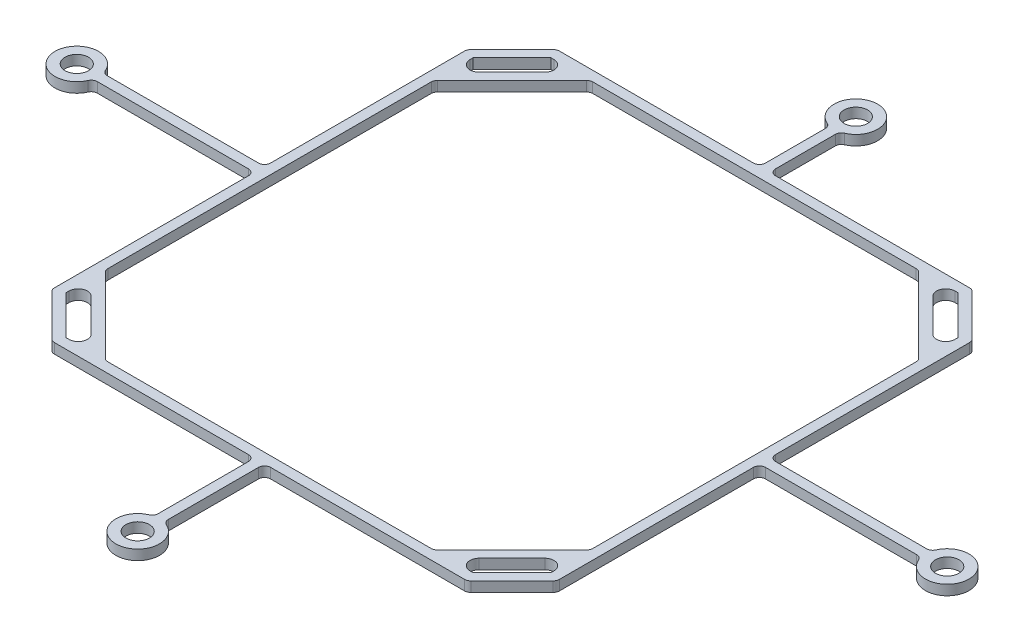
SolidWorks part; units mm, degrees
ref_plane "Front Plane" through (0, 0, 0) normal (0, 0, 1) x (1, 0, 0)
ref_plane "Top Plane" through (0, 0, 0) normal (0, 1, 0) x (1, 0, 0)
ref_plane "Right Plane" through (0, 0, 0) normal (1, 0, 0) x (0, 0, -1)
sketch "Sketch1" plane through (0, 0, 0) normal (0, 1, 0) x (1, 0, 0)
  line L0 (0, 0) -> (0, 56.4488) construction
  line L1 (0, 0) -> (-71.4488, 0) construction
  line L2 (-39.7988, 33.4083) -> (-33.4083, 39.7988)
  line L3 (-33.4083, -39.7988) -> (-29.2929, -39.7988)
  line L4 (-39.7988, -33.4083) -> (-39.7988, -29.2929)
  line L5 (-33.4083, 39.7988) -> (-29.2929, 39.7988)
  line L6 (39.7988, -33.4083) -> (39.7988, -29.2929)
  line L7 (-39.7988, -39.7988) -> (36.6035, 36.6035) construction
  line L8 (-36.6035, 36.6035) -> (39.7988, -39.7988) construction
  line L9 (33.4083, 39.7988) -> (39.7988, 33.4083)
  line L10 (39.7988, -33.4083) -> (33.4083, -39.7988)
  line L11 (-33.4083, -39.7988) -> (-39.7988, -33.4083)
  line L12 (-41.4488, 34.0917) -> (-34.0917, 41.4488)
  line L13 (34.0917, 41.4488) -> (0.825, 41.4488)
  line L14 (34.0917, 41.4488) -> (41.4488, 34.0917)
  line L15 (41.4488, -34.0917) -> (41.4488, -0.825)
  line L16 (41.4488, -34.0917) -> (34.0917, -41.4488)
  line L17 (-34.0917, -41.4488) -> (-0.825, -41.4488)
  line L18 (-34.0917, -41.4488) -> (-41.4488, -34.0917)
  line L19 (-41.4488, 34.0917) -> (-41.4488, 0.825)
  line L20 (-39.7988, 29.2929) -> (-29.2929, 39.7988)
  line L21 (-39.7988, 26.9594) -> (-26.9594, 39.7988)
  line L22 (29.2929, 39.7988) -> (39.7988, 29.2929)
  line L23 (26.9594, 39.7988) -> (39.7988, 26.9594)
  line L24 (39.7988, -29.2929) -> (29.2929, -39.7988)
  line L25 (39.7988, -26.9594) -> (26.9594, -39.7988)
  line L26 (-29.2929, -39.7988) -> (-39.7988, -29.2929)
  line L27 (-26.9594, -39.7988) -> (-39.7988, -26.9594)
  line L28 (-39.7988, 29.2929) -> (-39.7988, 33.4083)
  line L29 (-26.9594, 39.7988) -> (26.9594, 39.7988)
  line L30 (29.2929, 39.7988) -> (33.4083, 39.7988)
  line L31 (39.7988, 29.2929) -> (39.7988, 33.4083)
  line L32 (39.7988, -26.9594) -> (39.7988, 26.9594)
  line L33 (-39.7988, -26.9594) -> (-39.7988, 26.9594)
  line L34 (-26.9594, -39.7988) -> (26.9594, -39.7988)
  line L35 (29.2929, -39.7988) -> (33.4083, -39.7988)
  line L36 (67.9703, -0.825) -> (41.4488, -0.825)
  line L37 (0.825, 52.9703) -> (0.825, 41.4488)
  line L38 (-0.825, 52.9703) -> (-0.825, 41.4488)
  line L39 (67.9703, 0.825) -> (41.4488, 0.825)
  line L40 (-0.825, -57.9703) -> (-0.825, -41.4488)
  line L41 (0.825, -57.9703) -> (0.825, -41.4488)
  line L42 (-67.9703, 0.825) -> (-41.4488, 0.825)
  line L43 (-67.9703, -0.825) -> (-41.4488, -0.825)
  line L44 (0, 0) -> (0, -61.4488) construction
  line L45 (41.4488, 0.825) -> (41.4488, 34.0917)
  line L46 (-0.825, 41.4488) -> (-34.0917, 41.4488)
  line L47 (-41.4488, -0.825) -> (-41.4488, -34.0917)
  line L48 (0.825, -41.4488) -> (34.0917, -41.4488)
  arc A0 (0.825, 52.9703) -> (-0.825, 52.9703) centre (0, 56.4488) ccw
  circle A1 centre (0, 56.4488) radius 1.925
  circle A2 centre (71.4488, 0) radius 1.925
  arc A3 (67.9703, 0.825) -> (67.9703, -0.825) centre (71.4488, 0) cw
  arc A4 (-0.825, -57.9703) -> (0.825, -57.9703) centre (0, -61.4488) ccw
  circle A5 centre (0, -61.4488) radius 1.925
  arc A6 (-67.9703, 0.825) -> (-67.9703, -0.825) centre (-71.4488, 0) ccw
  circle A7 centre (-71.4488, 0) radius 1.925
  point P19 (0, 0)
  point P20 (0, 0)
  point P33 (0, 0)
  point P46 (0, 0)
  point P74 (0, 0)
  dimension "D10" = 3.85
  dimension "D11" = 1.65
  dimension "D15" = 1.65
  dimension "D16" = 3.85
  dimension "D20" = 3.85
  dimension "D21" = 1.65
  dimension "D1" = 1.65
  dimension "D2" = 79.5976
  dimension "D3" = 9.0376
  dimension "D5" = 1.65
  dimension "D6" = 4
  dimension "D7" = 2.91
  dimension "D8" = 1.65
  dimension "D12" = 0.825
  dimension "D13" = 0.825
  dimension "D14" = 15
  dimension "D17" = 30
  dimension "D18" = 0.825
  dimension "D19" = 0.825
  dimension "D22" = 0.825
  dimension "D23" = 0.825
  dimension "D24" = 20
  dimension "D25" = 12.8394
  dimension "D4" = 4
  dimension "D9" = 4
extrude "Boss-Extrude1" add sketch "Sketch1" along normal blind 1.65
fillet "Fillet4" radius 1 16 edges at (0.825, 0.825, -41.4488) (0.825, 0.825, -52.9703) (-0.825, 0.825, -52.9703) (-0.825, 0.825, -41.4488) (67.9703, 0.825, -0.825) (67.9703, 0.825, 0.825) (41.4488, 0.825, -0.825) (41.4488, 0.825, 0.825) (0.825, 0.825, 57.9703) (-0.825, 0.825, 57.9703) (-0.825, 0.825, 41.4488) (0.825, 0.825, 41.4488) (-41.4488, 0.825, 0.825) (-41.4488, 0.825, -0.825) (-67.9703, 0.825, 0.825) (-67.9703, 0.825, -0.825)
fillet "Fillet3" radius 1.5 8 edges at (29.2929, 0.825, 39.7988) (39.7988, 0.825, 29.2929) (-29.2929, 0.825, 39.7988) (-39.7988, 0.825, 29.2929) (-39.7988, 0.825, -29.2929) (-29.2929, 0.825, -39.7988) (39.7988, 0.825, -29.2929) (29.2929, 0.825, -39.7988)
fillet "Fillet5" radius 1 16 edges at (-26.9594, 0.825, 39.7988) (-39.7988, 0.825, 26.9594) (-41.4488, 0.825, 34.0917) (-34.0917, 0.825, 41.4488) (-39.7988, 0.825, -26.9594) (-26.9594, 0.825, -39.7988) (-41.4488, 0.825, -34.0917) (-34.0917, 0.825, -41.4488) (41.4488, 0.825, -34.0917) (34.0917, 0.825, -41.4488) (26.9594, 0.825, -39.7988) (39.7988, 0.825, -26.9594) (34.0917, 0.825, 41.4488) (41.4488, 0.825, 34.0917) (39.7988, 0.825, 26.9594) (26.9594, 0.825, 39.7988)
